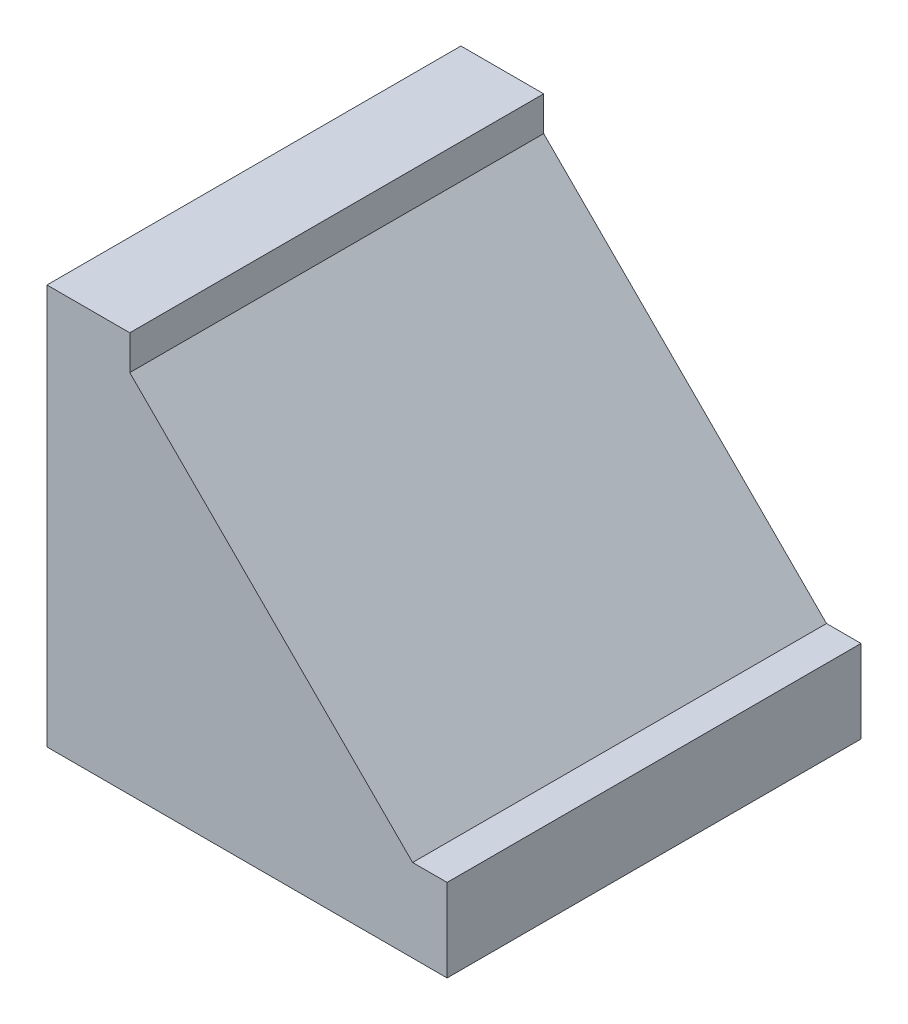
SolidWorks part; units mm, degrees
ref_plane "前视基准面" through (0, 0, 0) normal (0, 0, 1) x (1, 0, 0)
ref_plane "上视基准面" through (0, 0, 0) normal (0, 1, 0) x (1, 0, 0)
ref_plane "右视基准面" through (0, 0, 0) normal (1, 0, 0) x (0, 0, -1)
sketch "草图1" plane through (0, 0, 0) normal (0, 0, 1) x (1, 0, 0)
  line L0 (0, 58) -> (0, 0)
  line L1 (0, 0) -> (58, 0)
  line L2 (58, 0) -> (58, 12)
  line L3 (58, 12) -> (53, 12)
  line L4 (53, 12) -> (12, 53)
  line L5 (12, 53) -> (12, 58)
  line L6 (12, 58) -> (0, 58)
  dimension "D1" = 58
  dimension "D2" = 58
  dimension "D3" = 12
  dimension "D4" = 12
  dimension "D5" = 5
  dimension "D6" = 5
extrude "凸台-拉伸1" add sketch "草图1" along normal blind 60
